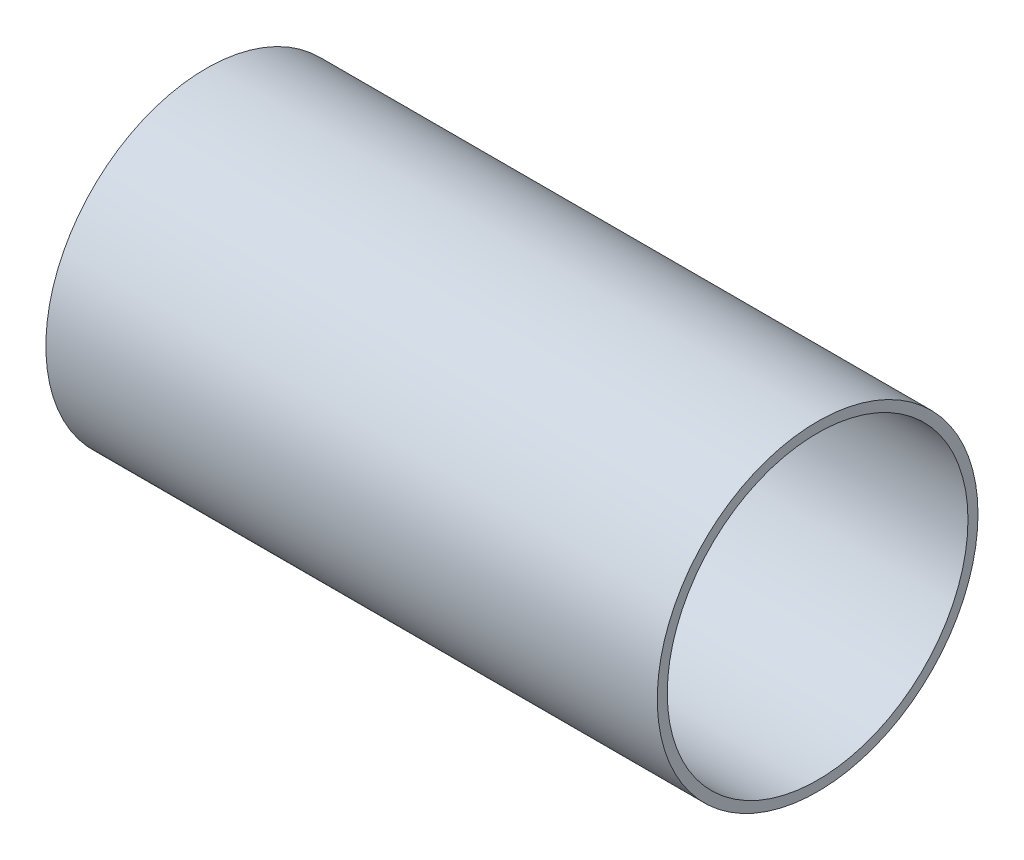
SolidWorks part; units mm, degrees
material "6061-T6 (SS)"
ref_plane "Front Plane" through (0, 0, 0) normal (0, 0, 1) x (1, 0, 0)
ref_plane "Top Plane" through (0, 0, 0) normal (0, 1, 0) x (1, 0, 0)
ref_plane "Right Plane" through (0, 0, 0) normal (1, 0, 0) x (0, 0, -1)
sketch "Sketch1" plane through (0, 0, 0) normal (1, 0, 0) x (0, 0, -1)
  circle A0 centre (0, 0) radius 101.6
  circle A1 centre (0, 0) radius 95.25
  dimension "D1" = 203.2
  dimension "D2" = 6.35
extrude "Boss-Extrude1" add sketch "Sketch1" along normal blind 387.35
